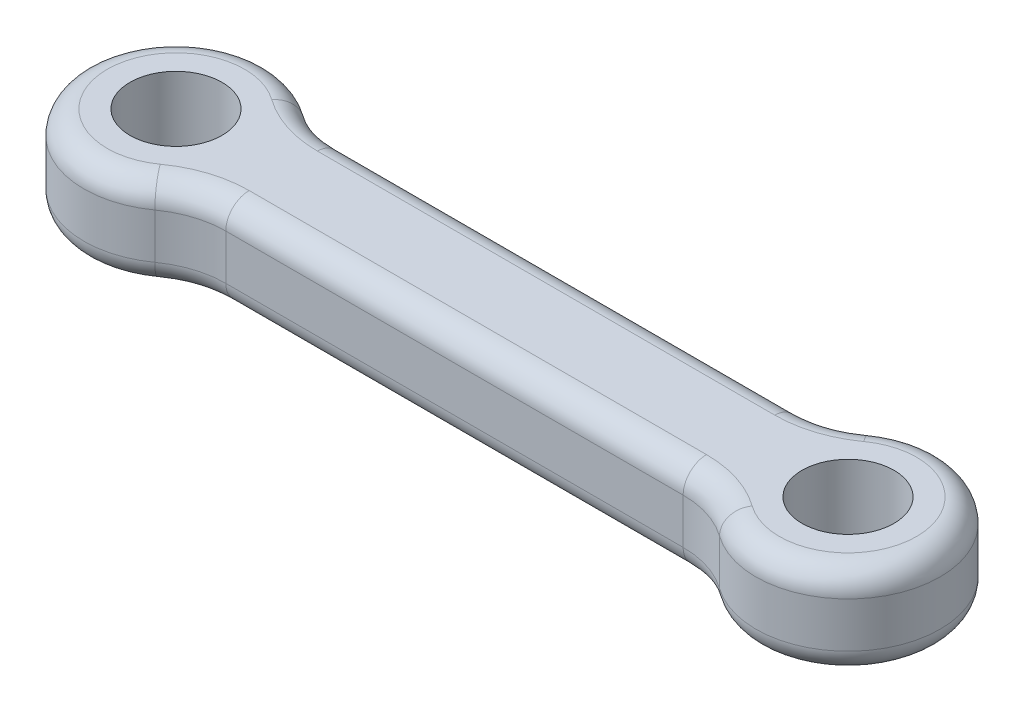
SolidWorks part; units mm, degrees
ref_plane "Front Plane" through (0, 0, 0) normal (0, 0, 1) x (1, 0, 0)
ref_plane "Top Plane" through (0, 0, 0) normal (0, 1, 0) x (1, 0, 0)
ref_plane "Right Plane" through (0, 0, 0) normal (1, 0, 0) x (0, 0, -1)
sketch "Sketch1" plane through (0, 0, 0) normal (0, 1, 0) x (1, 0, 0)
  line L0 (-18.25, 0) -> (18.25, 0) construction
  line L1 (-6.5908, -6.25) -> (43.0908, -6.25)
  line L2 (-6.5908, 6.25) -> (43.0908, 6.25)
  line L3 (-12.4204, -8.125) -> (-12.4204, 8.125) construction
  line L4 (-6.5908, -6.25) -> (-6.5908, 6.25) construction
  line L5 (18.25, -6.25) -> (18.25, 6.25) construction
  arc A0 (-12.4204, 8.125) -> (-12.4204, -8.125) centre (-18.25, 0) ccw
  arc A1 (-12.4204, -8.125) -> (-6.5908, -6.25) centre (-6.5908, -16.25) cw
  arc A2 (-12.4204, 8.125) -> (-6.5908, 6.25) centre (-6.5908, 16.25) ccw
  circle A3 centre (-18.25, 0) radius 5
  circle A4 centre (54.75, 0) radius 5
  arc A5 (48.9204, -8.125) -> (43.0908, -6.25) centre (43.0908, -16.25) ccw
  arc A6 (48.9204, 8.125) -> (48.9204, -8.125) centre (54.75, 0) cw
  arc A7 (48.9204, 8.125) -> (43.0908, 6.25) centre (43.0908, 16.25) cw
  dimension "D3" = 10
  dimension "D4" = 12.5
  dimension "D5" = 10
  dimension "D2" = 10
  dimension "D1" = 36.5
extrude "Boss-Extrude1" add sketch "Sketch1" along normal blind 10
fillet "Fillet1" radius 2.54 16 edges at (-28.25, 0, 0) (-9.6526, 0, 6.7303) (18.25, 0, 6.25) (46.1526, 0, 6.7303) (64.75, 0, 0) (46.1526, 0, -6.7303) (18.25, 0, -6.25) (-9.6526, 0, -6.7303) (18.25, 10, -6.25) (46.1526, 10, -6.7303) (64.75, 10, 0) (46.1526, 10, 6.7303) (18.25, 10, 6.25) (-9.6526, 10, 6.7303) (-28.25, 10, 0) (-9.6526, 10, -6.7303)
